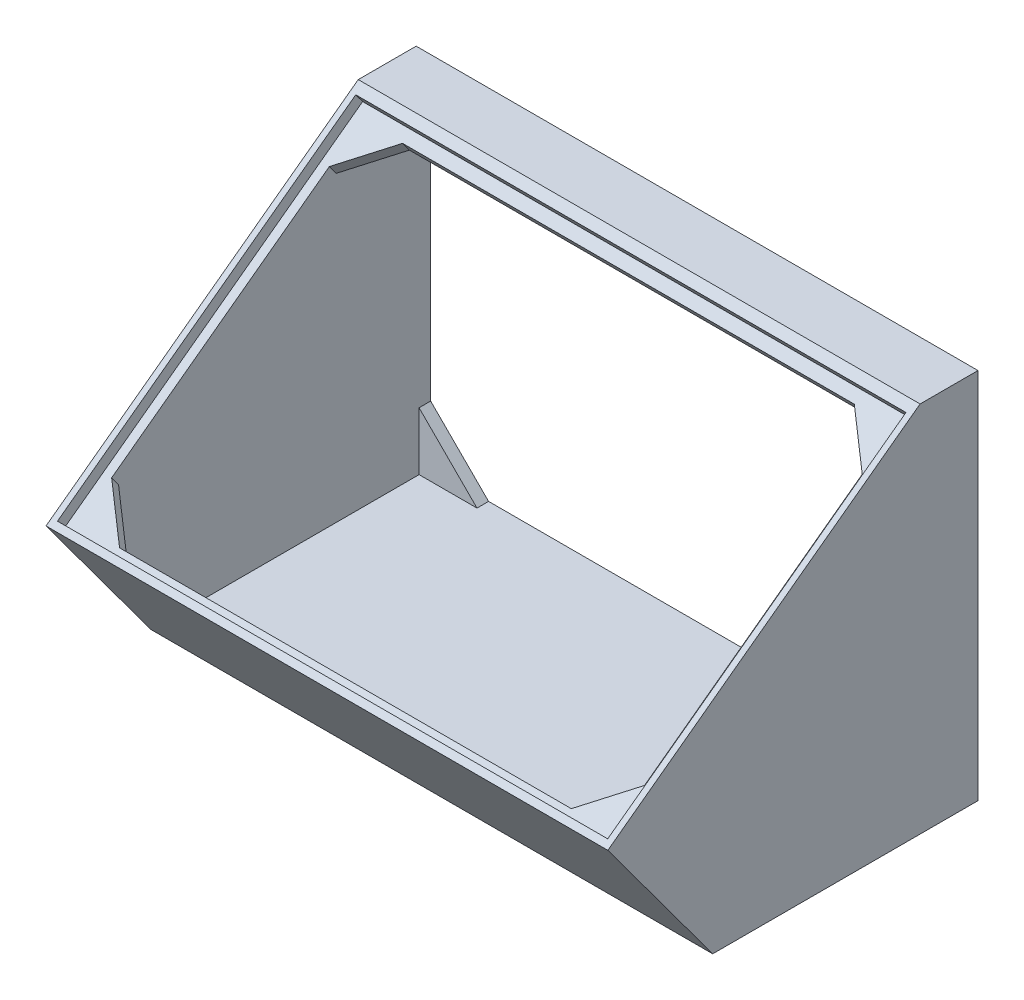
SolidWorks part; units mm, degrees
ref_plane "Front Plane" through (0, 0, 0) normal (0, 0, 1) x (1, 0, 0)
ref_plane "Top Plane" through (0, 0, 0) normal (0, 1, 0) x (1, 0, 0)
ref_plane "Right Plane" through (0, 0, 0) normal (1, 0, 0) x (0, 0, -1)
sketch "Sketch1" plane through (0, 0, 0) normal (1, 0, 0) x (0, 0, -1)
  line L0 (0, 0) -> (0, 45.25) construction
  line L1 (0, 41.4167) -> (-10, 41.4167)
  line L2 (-10, 41.4167) -> (-63.9114, 1.6353)
  line L3 (-63.9114, 1.6353) -> (-45.8056, -22.9016)
  line L4 (-45.8056, -22.9016) -> (0, -22.9016)
  line L5 (0, -22.9016) -> (0, 41.4167)
  point P10 (-68.8333, 57.75)
  dimension "D1" = 10
  dimension "D2" = 67
extrude "Boss-Extrude1" add sketch "Sketch1" along normal blind 97
shell "Shell1" thickness 2.5
sketch "Sketch2" plane through (0, 31.5932, 23.3127) normal (0, 0.8046, 0.5938) x (1, 0, 0)
  line L0 (1.8453, -17.2364) -> (95.155, -17.2364) construction
  line L3 (48.5, 12.3343) -> (48.5, -47.9552) construction
  line L4 (94.5, 12.3343) -> (2.5, 12.3343) construction
  line L5 (94.5, -47.9552) -> (2.5, -47.9552) construction
  line L7 (1.0001, -49.2364) -> (96.0001, -49.2364)
  line L8 (1.0001, -49.2364) -> (1.0001, 14.7636)
  line L9 (1.0001, 14.7636) -> (96.0001, 14.7636)
  line L10 (96.0001, -49.2364) -> (96.0001, 14.7636)
  line L11 (1.0001, -49.2364) -> (96.0001, 14.7636) construction
  line L12 (1.0001, 14.7636) -> (96.0001, -49.2364) construction
  point P12 (48.5001, -17.2364)
  dimension "D1" = 95
  dimension "D2" = 64
extrude "Cut-Extrude1" cut sketch "Sketch2" against normal blind 2 contours L8 L9 L10 L7
sketch "Sketch3" plane through (94.5, 0, 0) normal (-1, 0, 0) x (0, 0, 1)
  line L0 (11.855, 37.5623) -> (10.2457, 38.7498)
  line L1 (10.2457, 38.7498) -> (60.7123, 1.5103) construction
  line L2 (0, 38.9167) -> (10.3688, 38.9167) construction
  line L3 (11.855, 37.5623) -> (10.6675, 35.953)
  line L4 (10.6675, 35.953) -> (6.6512, 38.9167)
  line L6 (61.7431, 0.7497) -> (10.2457, 38.7498) construction
  line L7 (10.2457, 38.7498) -> (10.3688, 38.9167)
  line L8 (10.3688, 38.9167) -> (6.6512, 38.9167)
  dimension "D1" = 90
  dimension "D2" = 2
  dimension "D3" = 2
extrude "Boss-Extrude2" add sketch "Sketch3" along normal blind 93
sketch "Sketch4" plane through (0, 0, 0) normal (0, 0, -1) x (-1, 0, 0)
  line L0 (-94.5, -10.4016) -> (-84.5, -20.4016)
  line L2 (-94.5, -20.4016) -> (-2.5, -20.4016) construction
  line L3 (-84.5, -20.4016) -> (-94.5, -20.4016)
  line L4 (-94.5, -20.4016) -> (-94.5, -10.4016)
  line L5 (-84.5, 38.9167) -> (-94.5, 28.9167)
  line L6 (-94.5, 38.9167) -> (-2.5, 38.9167) construction
  line L7 (-94.5, -20.4016) -> (-94.5, 38.9167) construction
  line L8 (-94.5, 28.9167) -> (-94.5, 38.9167)
  line L9 (-94.5, 38.9167) -> (-84.5, 38.9167)
  line L10 (-2.5, 38.9167) -> (-2.5, 28.9167)
  line L11 (-2.5, 38.9167) -> (-2.5, 35.953) construction
  line L12 (-2.5, -20.4016) -> (-2.5, 38.9167) construction
  line L13 (-2.5, 28.9167) -> (-12.5, 38.9167)
  line L14 (-12.5, 38.9167) -> (-2.5, 38.9167)
  line L15 (-2.5, -20.4016) -> (-2.5, -10.4016)
  line L17 (-2.5, -10.4016) -> (-12.5, -20.4016)
  line L18 (-94.5, -20.4016) -> (-2.5, -20.4016) construction
  line L19 (-12.5, -20.4016) -> (-2.5, -20.4016)
  point P25 (0, 0)
  point P27 (0, 0)
  dimension "D1" = 10
  dimension "D2" = 10
  dimension "D3" = 10
  dimension "D4" = 10
  dimension "D5" = 10
  dimension "D6" = 10
  dimension "D7" = 10
  dimension "D8" = 10
extrude "Boss-Extrude3" add sketch "Sketch4" against normal blind 2
sketch "Sketch5" plane through (0, 29.9839, 22.1252) normal (0, 0.8046, 0.5938) x (1, 0, 0)
  line L0 (2.5, 12.7636) -> (2.5, 5.7636)
  line L1 (2.5, 12.7636) -> (2.5, -47.9552) construction
  line L2 (2.5, 5.7636) -> (9.5, 12.7636)
  line L3 (2.5, 12.7636) -> (94.5, 12.7636) construction
  line L4 (9.5, 12.7636) -> (2.5, 12.7636)
  line L5 (2.5, -47.9552) -> (9.5, -47.9552)
  line L6 (94.5, -47.9552) -> (2.5, -47.9552) construction
  line L7 (9.5, -47.9552) -> (2.5, -40.9552)
  line L8 (2.5, -40.9552) -> (2.5, -47.9552)
  line L9 (94.5, -47.9552) -> (94.5, -40.9552)
  line L10 (94.5, -47.9552) -> (94.5, -13.7228) construction
  line L11 (94.5, -40.9552) -> (87.5, -47.9552)
  line L12 (2.5, -47.9552) -> (94.5, -47.9552) construction
  line L13 (87.5, -47.9552) -> (94.5, -47.9552)
  line L14 (94.5, 12.7636) -> (94.5, 5.7636)
  line L15 (94.5, 12.7636) -> (94.5, -47.9552) construction
  line L16 (94.5, 5.7636) -> (87.5, 12.7636)
  line L17 (87.5, 12.7636) -> (94.5, 12.7636)
  dimension "D1" = 7
  dimension "D2" = 7
  dimension "D3" = 7
  dimension "D4" = 7
  dimension "D5" = 7
  dimension "D6" = 7
extrude "Boss-Extrude4" add sketch "Sketch5" against normal blind 2
